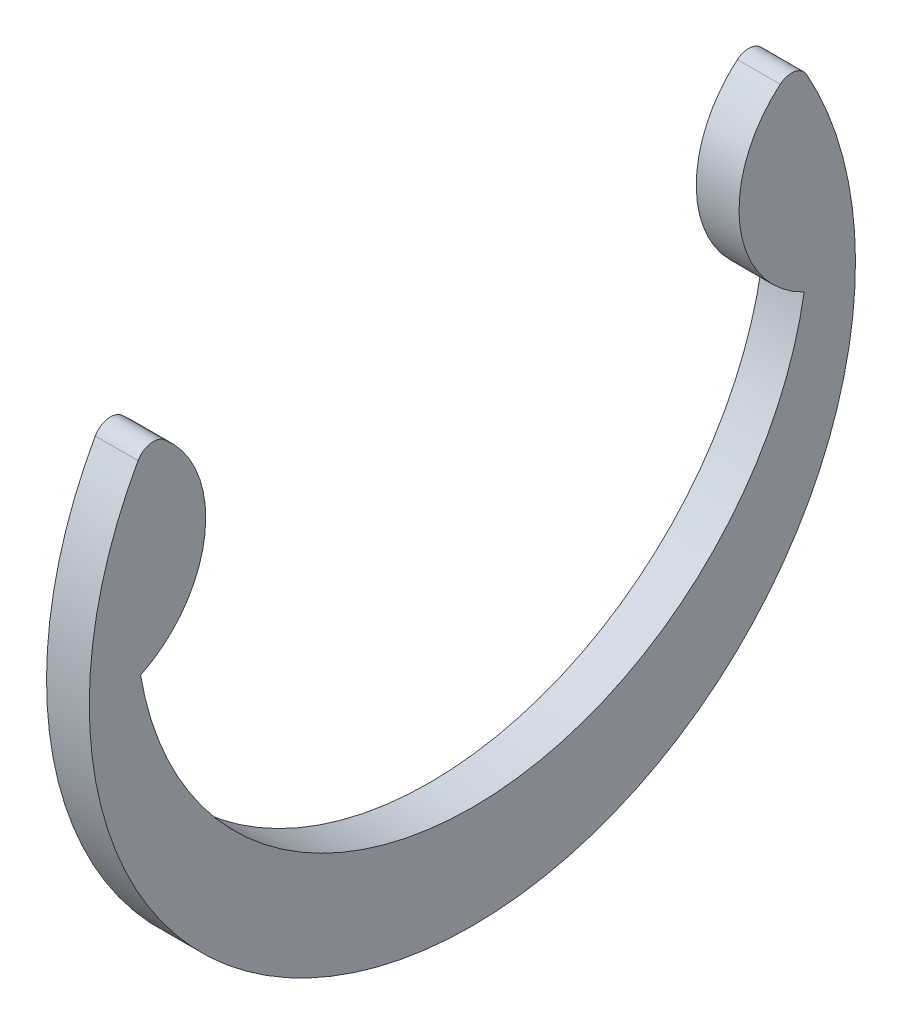
SolidWorks part; units mm, degrees
material "Cast Carbon Steel"
ref_plane "Front" through (0, 0, 0) normal (0, 0, 1) x (1, 0, 0)
ref_plane "Top" through (0, 0, 0) normal (0, 1, 0) x (1, 0, 0)
ref_plane "Right" through (0, 0, 0) normal (1, 0, 0) x (0, 0, -1)
sketch "Sketch1" plane through (0, 0, 0) normal (1, 0, 0) x (0, 0, -1)
  circle A0 centre (0, 0) radius 4.1656 construction
  arc A1 (-4.9276, 0) -> (4.9276, 0) centre (0, 0.8317) ccw
  circle A2 centre (0, 0) radius 5.6896 construction
  circle A3 centre (0, 0) radius 5.969 construction
  arc A4 (4.9658, 2.7771) -> (-4.9658, 2.7771) centre (0, 0) cw
  arc A5 (-4.5718, 2.8495) -> (-4.9276, 0) centre (-5.6691, 1.5395) cw
  arc A6 (-4.9658, 2.7771) -> (-4.5718, 2.8495) centre (-4.7388, 2.6501) cw
  arc A7 (4.9658, 2.7771) -> (4.5718, 2.8495) centre (4.7388, 2.6501) ccw
  arc A8 (4.9276, 0) -> (4.5718, 2.8495) centre (5.6691, 1.5395) cw
  arc A9 (4.5718, 2.8495) -> (4.9276, 0) centre (0, 0.8317) cw construction
  dimension "A" = 8.3312
  dimension "OD" = 11.3792
  dimension "D1" = 2.7771
  dimension "D2" = 9.8552
extrude "Extrude1" add sketch "Sketch1" along normal mid plane 0.635
sketch "Sketch2" plane through (0, 0, 0) normal (0, 0, 1) x (1, 0, 0)
  line L0 (-1.8415, 0) -> (5.5245, 0)
  line L1 (5.5245, 0) -> (5.5245, -4.7625)
  line L3 (5.5245, -4.7625) -> (0.3683, -4.7625)
  line L4 (0.3683, -4.7625) -> (0.3683, -4.2545)
  line L5 (0.3683, -4.2545) -> (-0.3683, -4.2545)
  line L6 (-0.3683, -4.2545) -> (-0.3683, -4.7625)
  line L7 (-0.3683, -4.7625) -> (-1.8415, -4.7625) construction
  line L8 (-1.8415, -4.7625) -> (-1.8415, 0) construction
  line L9 (0, -4.2545) -> (0, 0) construction
  line L10 (5.5245, 0) -> (14.0551, 0) construction
  line L11 (-0.3683, -4.7625) -> (-1.5875, -4.7625)
  line L12 (-1.5875, -4.7625) -> (-1.8415, -4.5085)
  line L13 (-1.8415, -4.5085) -> (-1.8415, 0)
  point P14 (-0.3683, -4.5085)
  dimension "D2" = 7.366
  dimension "D3" = 1.8415
  dimension "D4" = 45
revolve "Revolve1" [suppressed] add sketch "Sketch2" angle 360 about L10
equation "\"D2@Sketch2\" = \"W@Sketch2\"*10"
equation "\"D3@Sketch2\" = \"D2@Sketch2\"/4"
equation "\"D1@Sketch1\" = \"A@Sketch1\"/3"
equation "\"D2@Sketch1\" = (\"OD@Sketch1\"+\"A@Sketch1\")/2"
